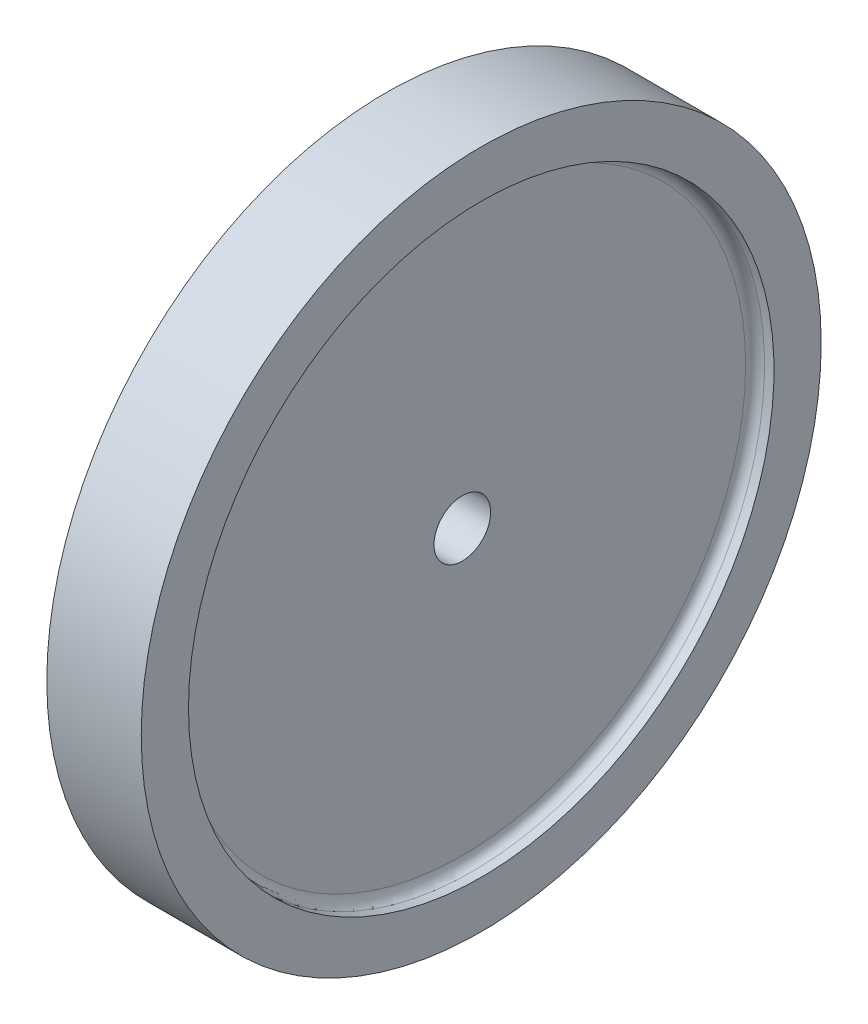
SolidWorks part; units mm, degrees
ref_plane "Plan de face" through (0, 0, 0) normal (0, 0, 1) x (1, 0, 0)
ref_plane "Plan de dessus" through (0, 0, 0) normal (0, 1, 0) x (1, 0, 0)
ref_plane "Plan de droite" through (0, 0, 0) normal (1, 0, 0) x (0, 0, -1)
sketch "Esquisse1" plane through (0, 0, 0) normal (0, 0, 1) x (1, 0, 0)
  line L0 (-3, 31) -> (-5, 31)
  line L1 (-3, 0) -> (3, 0)
  line L2 (-3, 0) -> (-3, 31)
  line L4 (3, 0) -> (3, 31)
  line L5 (-5, 31) -> (-5, 36)
  line L6 (-5, 36) -> (5, 36)
  line L7 (5, 36) -> (5, 31)
  line L8 (5, 31) -> (3, 31)
  line L9 (0, 0) -> (0, 79.5434) construction
  dimension "D1" = 10
  dimension "D2" = 5
  dimension "D3" = 3
  dimension "D4" = 6
  dimension "D5" = 36
  dimension "D6" = 5
revolve "Révolution1" add sketch "Esquisse1" angle 360 about L1
sketch "Esquisse2" plane through (3, 0, 0) normal (1, 0, 0) x (0, 0, -1)
  circle A0 centre (0, 0) radius 3
  dimension "D1" = 6
extrude "Enlèv. mat.-Extru.2" cut sketch "Esquisse2" against normal through all
fillet "Congé1" radius 1 2 edges at (-3, 0, 31) (3, 0, 31)
equation "\"D2@Esquisse1\"=\"D1@Esquisse1\"/2"
equation "\"D4@Esquisse1\"=\"D3@Esquisse1\"+\"D3@Esquisse1\""
